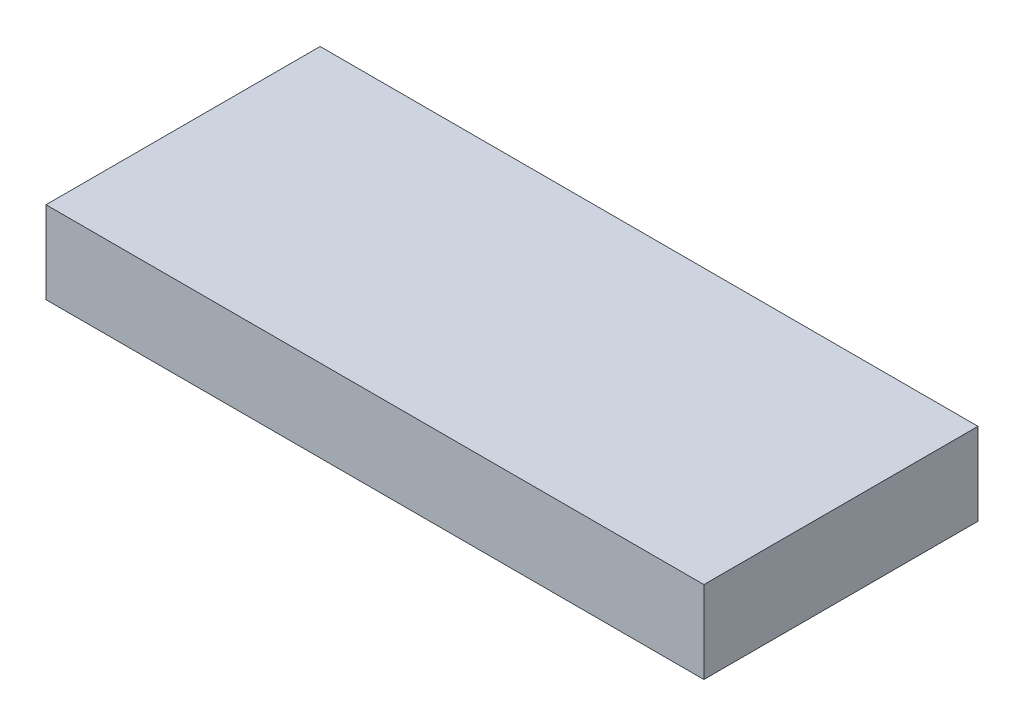
SolidWorks part; units mm, degrees
ref_plane "Front Plane" through (0, 0, 0) normal (0, 0, 1) x (1, 0, 0)
ref_plane "Top Plane" through (0, 0, 0) normal (0, 1, 0) x (1, 0, 0)
ref_plane "Right Plane" through (0, 0, 0) normal (1, 0, 0) x (0, 0, -1)
sketch "Sketch1" plane through (0, 0, 0) normal (0, 1, 0) x (1, 0, 0)
  line L1 (-35.9516, 14.2134) -> (0.0484, 14.2134)
  line L2 (-35.9516, 14.2134) -> (-35.9516, -0.7866)
  line L3 (-35.9516, -0.7866) -> (0.0484, -0.7866)
  line L4 (0.0484, 14.2134) -> (0.0484, -0.7866)
  dimension "D1" = 36
  dimension "D2" = 15
extrude "Boss-Extrude1" add sketch "Sketch1" along normal blind 4.5
